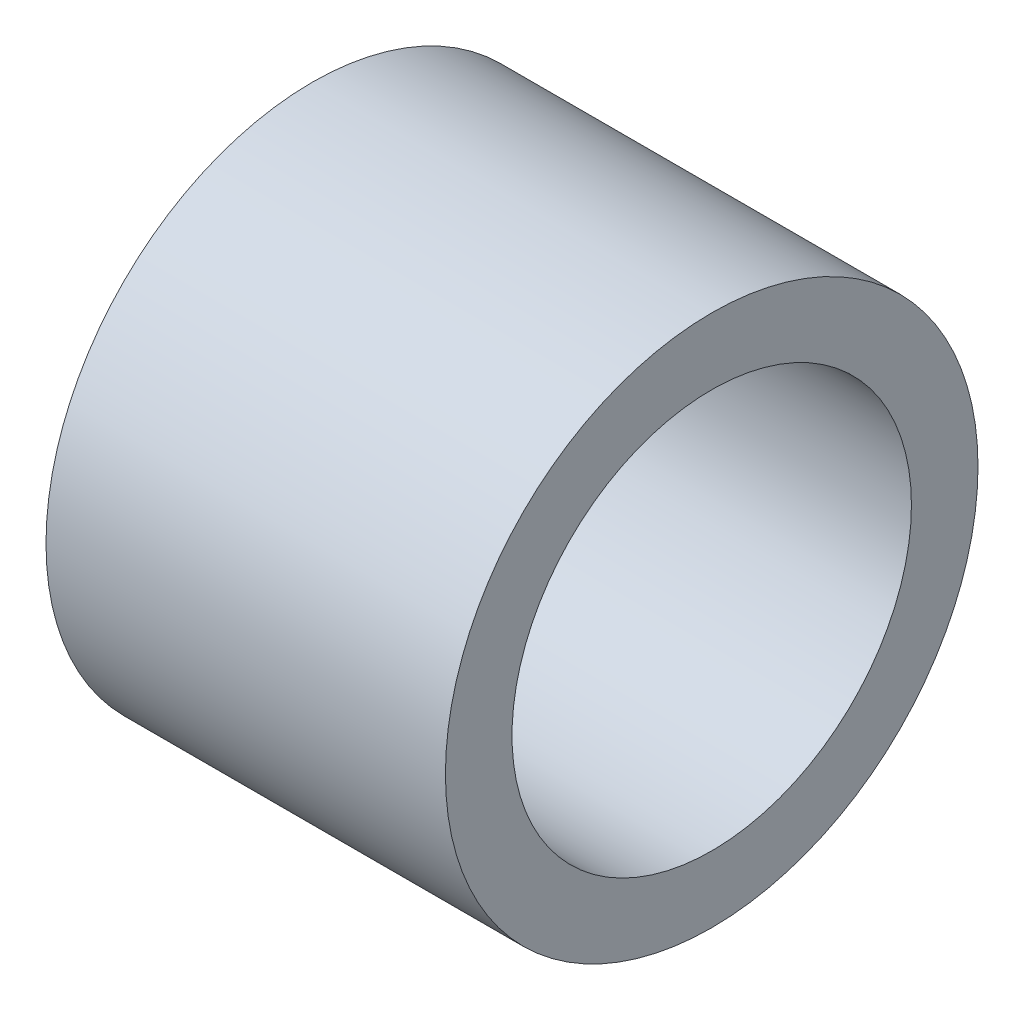
SolidWorks part; units mm, degrees
ref_plane "Front Plane" through (0, 0, 0) normal (0, 0, 1) x (1, 0, 0)
ref_plane "Top Plane" through (0, 0, 0) normal (0, 1, 0) x (1, 0, 0)
ref_plane "Right Plane" through (0, 0, 0) normal (1, 0, 0) x (0, 0, -1)
sketch "Sketch1" plane through (0, 0, 0) normal (1, 0, 0) x (0, 0, -1)
  circle A0 centre (0, 0) radius 9.525
  circle A1 centre (0, 0) radius 12.7
  dimension "D1" = 19.05
  dimension "D2" = 25.4
extrude "Boss-Extrude1" add sketch "Sketch1" along normal mid plane 19.05
